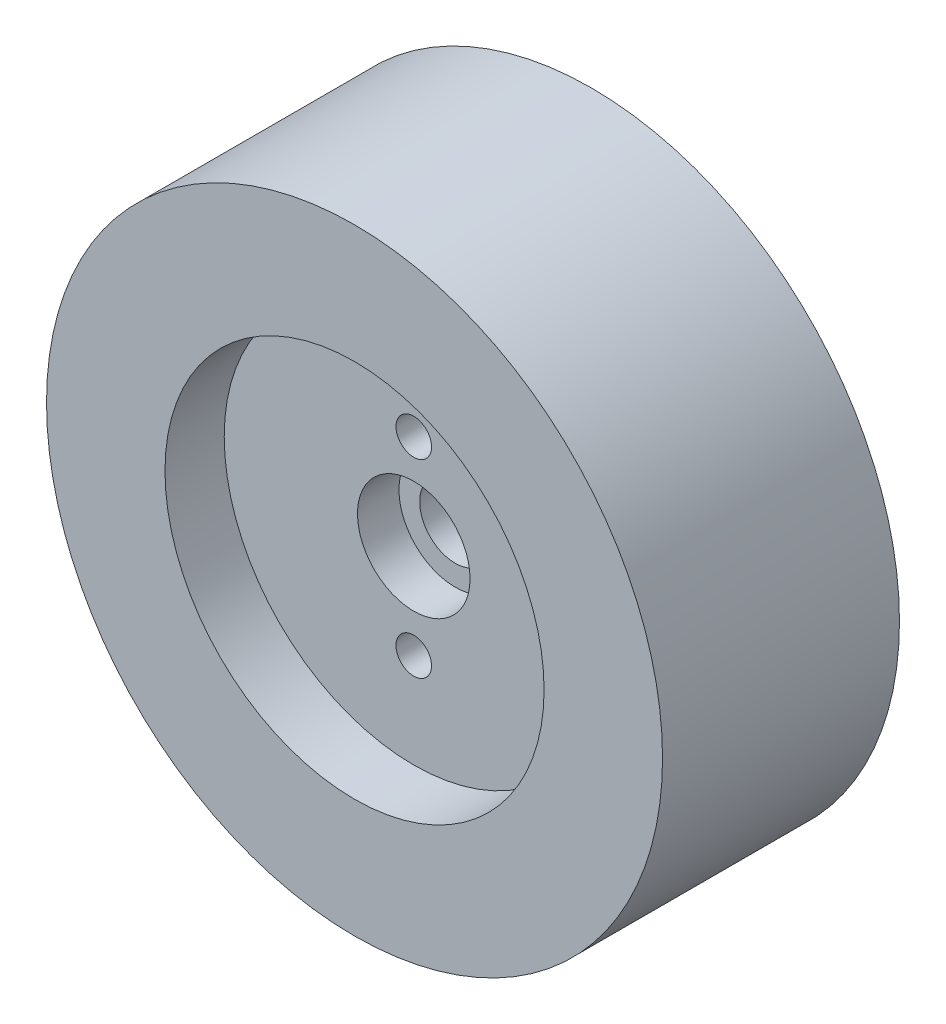
SolidWorks part; units mm, degrees
material "BUTYL"
ref_plane "Plan de face" through (0, 0, 0) normal (0, 0, 1) x (1, 0, 0)
ref_plane "Plan de dessus" through (0, 0, 0) normal (0, 1, 0) x (1, 0, 0)
ref_plane "Plan de droite" through (0, 0, 0) normal (1, 0, 0) x (0, 0, -1)
sketch "Esquisse1" plane through (0, 0, 0) normal (0, 0, 1) x (1, 0, 0)
  circle A0 centre (0, 0) radius 3
  circle A1 centre (0, 0) radius 26
  dimension "D1" = 6
  dimension "D2" = 52
extrude "Boss.-Extru.1" add sketch "Esquisse1" along normal blind 20
sketch "Esquisse2" plane through (0, 0, 20) normal (0, 0, 1) x (1, 0, 0)
  circle A0 centre (0, 0) radius 16
  dimension "D1" = 32
extrude "Enlèv. mat.-Extru.1" cut sketch "Esquisse2" against normal blind 5
sketch "Esquisse3" plane through (0, 0, 15) normal (0, 0, 1) x (1, 0, 0)
  circle A0 centre (0, 0) radius 4.75
  dimension "D1" = 9.5
extrude "Enlèv. mat.-Extru.2" cut sketch "Esquisse3" against normal blind 3.5
sketch "Esquisse4" plane through (0, 0, 15) normal (0, 0, 1) x (1, 0, 0)
  circle A0 centre (0, 8) radius 1.5
  circle A1 centre (0, -8) radius 1.5
  dimension "D1" = 3
  dimension "D2" = 3
  dimension "D3" = 8
  dimension "D4" = 8
extrude "Enlèv. mat.-Extru.3" cut sketch "Esquisse4" against normal through all
